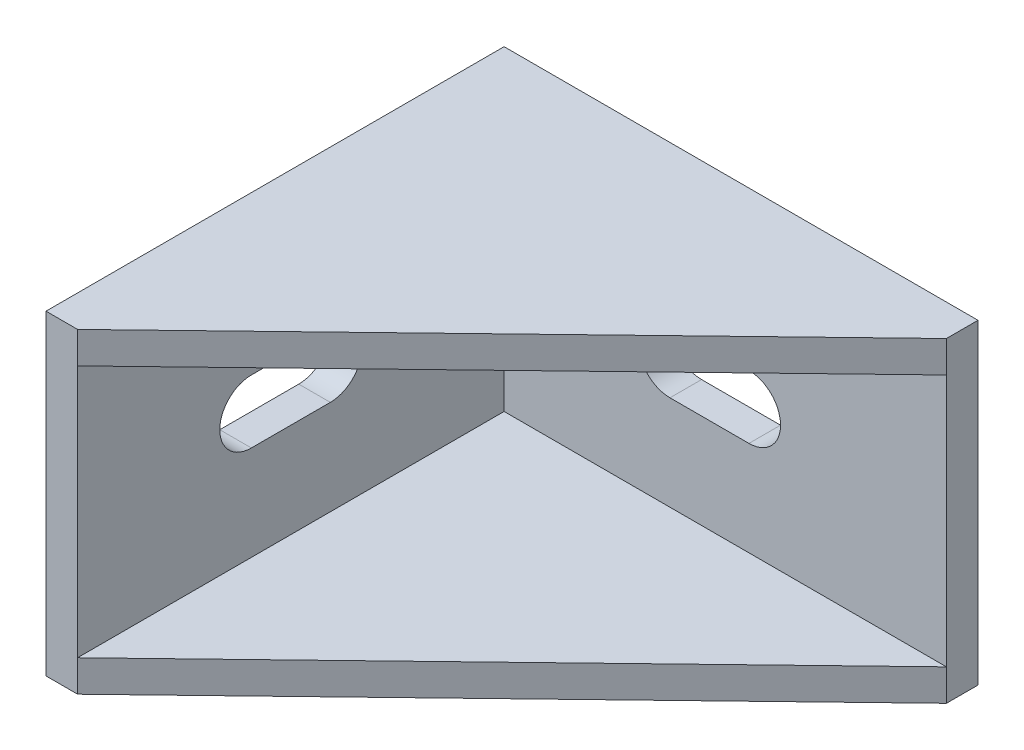
SolidWorks part; units mm, degrees
ref_plane "Plan de face" through (0, 0, 0) normal (0, 0, 1) x (1, 0, 0)
ref_plane "Plan de dessus" through (0, 0, 0) normal (0, 1, 0) x (1, 0, 0)
ref_plane "Plan de droite" through (0, 0, 0) normal (1, 0, 0) x (0, 0, -1)
sketch "Esquisse1" plane through (0, 0, 0) normal (0, 0, 1) x (1, 0, 0)
  line L1 (-15, -10) -> (15, -10)
  line L2 (-15, -10) -> (-15, 10)
  line L3 (-15, 10) -> (15, 10)
  line L4 (15, -10) -> (15, 10)
  line L5 (-15, -10) -> (15, 10) construction
  line L6 (-15, 10) -> (15, -10) construction
  point P0 (0, 0)
  dimension "D1" = 30
  dimension "D2" = 20
extrude "Boss.-Extru.1" add sketch "Esquisse1" along normal blind 2
sketch "Esquisse2" plane through (0, 0, 2) normal (0, 0, 1) x (1, 0, 0)
  line L3 (-13, 10) -> (-13, -10)
  line L4 (15, 10) -> (-15, 10) construction
  line L5 (-15, -10) -> (15, -10) construction
  line L6 (-15, 10) -> (-13, 10)
  line L7 (-13, -10) -> (-15, -10)
  line M4 (15, 10) -> (-15, 10)
  line M5 (-15, 10) -> (-15, -10)
  line M6 (-15, -10) -> (15, -10)
  dimension "D3" = 2
extrude "Boss.-Extru.2" add sketch "Esquisse2" along normal blind 27 contours L3 M4 M5 M6
sketch "Esquisse3" plane through (0, 0, 2) normal (0, 0, 1) x (1, 0, 0)
  line L0 (-2.5, 0) -> (2.5, 0) construction
  line L1 (-2.5, 2) -> (2.5, 2)
  line L2 (-2.5, -2) -> (2.5, -2)
  arc A0 (-2.5, 2) -> (-2.5, -2) centre (-2.5, 0) ccw
  arc A1 (2.5, -2) -> (2.5, 2) centre (2.5, 0) ccw
  point P2 (0, 0)
  dimension "D1" = 4
  dimension "D2" = 5
extrude "Enlèv. mat.-Extru.1" cut sketch "Esquisse3" against normal blind 27
sketch "Esquisse4" plane through (-13, 0, 0) normal (1, 0, 0) x (0, 0, -1)
  line L0 (-29, 10) -> (-2, -10) construction
  line L1 (-18, 0) -> (-13, 0) construction
  line L2 (-18, 2) -> (-13, 2)
  line L3 (-18, -2) -> (-13, -2)
  arc A0 (-18, 2) -> (-18, -2) centre (-18, 0) ccw
  arc A1 (-13, -2) -> (-13, 2) centre (-13, 0) ccw
  point P6 (-15.5, 0)
  dimension "D1" = 5
  dimension "D2" = 4
extrude "Enlèv. mat.-Extru.2" cut sketch "Esquisse4" against normal blind 27
sketch "Esquisse5" plane through (0, -10, 0) normal (0, -1, 0) x (-1, 0, 0)
  line L0 (13, -29) -> (-15, -2)
  line L1 (13, -29) -> (13, -2)
  line L2 (13, -2) -> (-15, -2)
extrude "Boss.-Extru.3" add sketch "Esquisse5" against normal blind 2
sketch "Esquisse6" plane through (0, 10, 0) normal (0, 1, 0) x (1, 0, 0)
  line L0 (15, -2) -> (-13, -29)
  line L1 (-13, -29) -> (-13, -2)
  line L2 (-13, -2) -> (15, -2)
extrude "Boss.-Extru.4" add sketch "Esquisse6" against normal blind 2
sketch "Esquisse7" plane through (0, 0, 0) normal (0, 0, -1) x (-1, 0, 0)
  line L0 (-4.5, 0) -> (-15, 0) construction
  line L1 (-15, -10) -> (-15, 10) construction
  line L2 (4.5, 0) -> (15, 0) construction
  line L3 (15, 10) -> (15, -10) construction
  line L4 (-9.75, -1) -> (-9.75, 1) construction
  line L5 (-11.75, -1) -> (-11.75, 1)
  line L6 (-7.75, -1) -> (-7.75, 1)
  line L7 (9.75, -1) -> (9.75, 1) construction
  line L8 (7.75, -1) -> (7.75, 1)
  line L9 (11.75, -1) -> (11.75, 1)
  arc A0 (-2.5, 2) -> (-2.5, -2) centre (-2.5, 0) ccw construction
  arc A1 (2.5, -2) -> (2.5, 2) centre (2.5, 0) ccw construction
  arc A2 (-11.75, -1) -> (-7.75, -1) centre (-9.75, -1) ccw
  arc A3 (-7.75, 1) -> (-11.75, 1) centre (-9.75, 1) ccw
  arc A4 (7.75, -1) -> (11.75, -1) centre (9.75, -1) ccw
  arc A5 (11.75, 1) -> (7.75, 1) centre (9.75, 1) ccw
  point P16 (-9.75, 0)
  point P22 (9.75, 0)
  point P28 (-9.75, 3)
  point P29 (-9.75, -3)
  point P30 (9.75, 3)
  point P31 (9.75, -3)
  dimension "D1" = 6
  dimension "D2" = 4
  dimension "D3" = 4
  dimension "D4" = 6
extrude "Boss.-Extru.5" add sketch "Esquisse7" along normal blind 3
fillet "Congé2" radius 0.5 4 edges at (7.75, 0, -3) (9.75, -3, -3) (11.75, 0, -3) (9.75, 3, -3)
fillet "Congé3" radius 0.5 4 edges at (-11.75, 0, -3) (-9.75, -3, -3) (-7.75, 0, -3) (-9.75, 3, -3)
